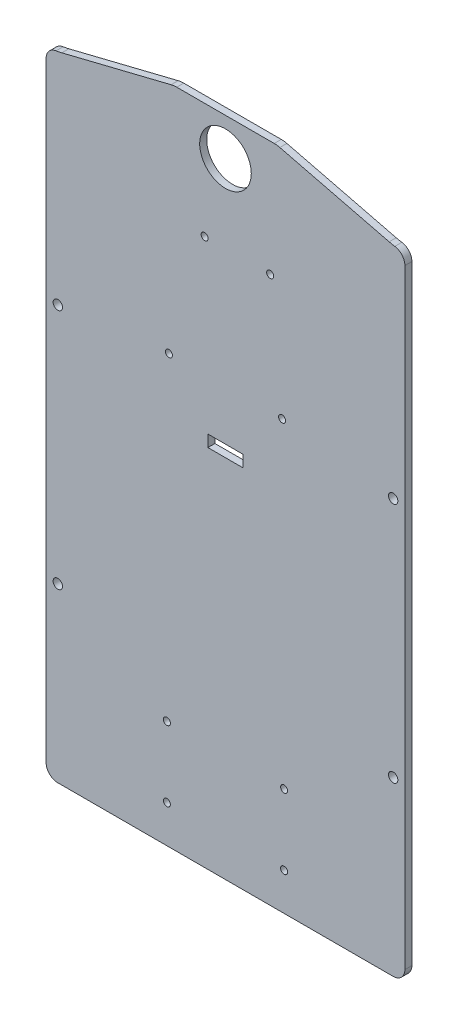
SolidWorks part; units mm, degrees
ref_plane "Alzado" through (0, 0, 0) normal (0, 0, 1) x (1, 0, 0)
ref_plane "Planta" through (0, 0, 0) normal (0, 1, 0) x (1, 0, 0)
ref_plane "Vista lateral" through (0, 0, 0) normal (1, 0, 0) x (0, 0, -1)
sketch "Croquis1" plane through (0, 0, 0) normal (0, 0, 1) x (1, 0, 0)
  line L1 (-76.5, 135) -> (76.5, 135)
  line L2 (-76.5, 135) -> (-76.5, -135)
  line L3 (-76.5, -135) -> (76.5, -135)
  line L4 (76.5, 135) -> (76.5, -135)
  line L5 (-76.5, 135) -> (76.5, -135) construction
  line L6 (-76.5, -135) -> (76.5, 135) construction
  point P0 (0, 0)
  dimension "D1" = 270
  dimension "D2" = 153
extrude "Saliente-Extruir1" add sketch "Croquis1" along normal blind 3
sketch "Croquis2" plane through (0, 0, 3) normal (0, 0, 1) x (1, 0, 0)
  line L0 (0, 135) -> (0, -135) construction
  line L1 (76.5, 135) -> (-76.5, 135) construction
  line L2 (-76.5, -135) -> (76.5, -135) construction
  line L3 (-76.5, 0) -> (-76.5, -10) construction
  line L4 (-76.5, 135) -> (-76.5, -135) construction
  line L5 (-76.5, 110) -> (0, 110) construction
  line L6 (-76.5, 0) -> (-76.5, 41.5) construction
  line L7 (-76.5, 41.5) -> (-71.5, 41.5) construction
  line L8 (76.5, -135) -> (76.5, 135) construction
  line L10 (0, -10) -> (76.5, -10) construction
  circle A8 centre (-71.5, 41.5) radius 2
  circle A9 centre (-71.5, -61.5) radius 2
  circle A10 centre (71.5, -61.5) radius 2
  circle A11 centre (71.5, 41.5) radius 2
  dimension "D2" = 4
  dimension "D6" = 51.5
  dimension "D1" = 125
  dimension "D3" = 5
  dimension "D4" = 5
  dimension "D5" = 5
extrude "Cortar-Extruir1" cut sketch "Croquis2" against normal through all
fillet "Redondeo1" radius 5 4 edges at (-76.5, -135, 1.5) (76.5, -135, 1.5) (76.5, 135, 1.5) (-76.5, 135, 1.5)
sketch "Croquis4" plane through (0, 0, 3) normal (0, 0, 1) x (1, 0, 0)
  line L0 (0, 0) -> (76.5, 0) construction
  line L1 (76.5, -130) -> (76.5, 130) construction
  line L2 (0, 0) -> (0, 135) construction
  line L3 (71.5, 135) -> (-71.5, 135) construction
  line L4 (-60, 113.7625) -> (-60, 106.2375) construction
  line L5 (-60, 110) -> (0, 110) construction
  line L6 (-76.5, 130) -> (-76.5, -130) construction
  line L7 (-76.5, 114.7625) -> (76.5, 114.7625) construction
  line L8 (-76.5, 114.7625) -> (-76.5, 105.2375) construction
  line L9 (-76.5, 105.2375) -> (76.5, 105.2375) construction
  line L10 (76.5, 114.7625) -> (76.5, 105.2375) construction
  line L11 (-76.5, 114.7625) -> (76.5, 105.2375) construction
  line L12 (-76.5, 105.2375) -> (76.5, 114.7625) construction
  line L13 (0, 135) -> (0, 147.2375) construction
  line L14 (22, 147.2375) -> (-22, 147.2375)
  line L15 (-22, 147.2375) -> (-71.5, 135)
  line L16 (22, 147.2375) -> (71.5, 135)
  line L17 (-71.5, 135) -> (71.5, 135)
  circle A0 centre (0, 129.7625) radius 11 construction
  dimension "D2" = 22
  dimension "D1" = 9.525
  dimension "D3" = 42
  dimension "D4" = 15
  dimension "D5" = 22
extrude "Saliente-Extruir2" add sketch "Croquis4" against normal up to surface (3 mm away) up to face at (69.5, 41.5, 0)
fillet "Redondeo2" radius 25 2 edges at (71.5, 135, 1.5) (-71.5, 135, 1.5)
fillet "Redondeo3" radius 10 2 edges at (22, 147.2375, 1.5) (-22, 147.2375, 1.5)
sketch "Croquis5" plane through (0, 0, 3) normal (0, 0, 1) x (1, 0, 0)
  line L0 (0, 0) -> (0, 147.2375) construction
  line L1 (20.7822, 147.2375) -> (-20.7822, 147.2375) construction
  line L2 (-60, 113.7625) -> (-60, 106.2375) construction
  line L3 (-60, 110) -> (0, 110) construction
  line L4 (-76.5, 130) -> (-76.5, -130) construction
  line L5 (-76.5, 114.7625) -> (76.5, 114.7625) construction
  line L6 (-76.5, 114.7625) -> (-76.5, 105.2375) construction
  line L7 (-76.5, 105.2375) -> (76.5, 105.2375) construction
  line L8 (76.5, 114.7625) -> (76.5, 105.2375) construction
  line L9 (-76.5, 114.7625) -> (76.5, 105.2375) construction
  line L10 (-76.5, 105.2375) -> (76.5, 114.7625) construction
  line L12 (-20, 146.2375) -> (20, 146.2375) construction
  line L13 (-20, 146.2375) -> (-20, 116.2375) construction
  line L14 (-20, 116.2375) -> (20, 116.2375) construction
  line L15 (20, 146.2375) -> (20, 116.2375) construction
  line L16 (-20, 146.2375) -> (20, 116.2375) construction
  line L17 (-20, 116.2375) -> (20, 146.2375) construction
  circle A0 centre (0, 131.2375) radius 11
  dimension "D2" = 26
  dimension "D3" = 22
  dimension "D1" = 9.525
  dimension "D4" = 30
  dimension "D5" = 40
extrude "Cortar-Extruir3" cut sketch "Croquis5" against normal through all
sketch "Croquis6" plane through (0, 0, 3) normal (0, 0, 1) x (1, 0, 0)
  line L0 (24.13, 98.0201) -> (24.13, 47.2201) construction
  line L1 (0, 147.2375) -> (0, 0) construction
  line L2 (20.7822, 147.2375) -> (-20.7822, 147.2375) construction
  line L3 (-24.13, 47.2201) -> (24.13, 47.2201) construction
  line L5 (-7.5, 25.7977) -> (7.5, 25.7977)
  line L6 (-7.5, 25.7977) -> (-7.5, 20.7977)
  line L7 (-7.5, 20.7977) -> (7.5, 20.7977)
  line L8 (7.5, 25.7977) -> (7.5, 20.7977)
  circle A0 centre (-8.89, 98.0201) radius 1.5
  circle A1 centre (19.05, 98.0201) radius 1.5
  circle A2 centre (24.13, 47.2201) radius 1.5
  circle A3 centre (-24.13, 47.2201) radius 1.5
  point P13 (0, 47.2201)
  point P19 (0, 20.7977)
  dimension "D1" = 27.94
  dimension "D3" = 48.26
  dimension "D5" = 3
  dimension "D6" = 3
  dimension "D7" = 3
  dimension "D8" = 3
  dimension "D2" = 5.08
  dimension "D4" = 50.8
  dimension "D9" = 15
  dimension "D10" = 5
extrude "Cortar-Extruir4" cut sketch "Croquis6" against normal through all
sketch "Croquis7" plane through (0, 0, 3) normal (0, 0, 1) x (1, 0, 0)
  line L0 (0, 147.2375) -> (0, -135) construction
  line L1 (-25, -89.0384) -> (25, -89.0384) construction
  line L2 (-25, -89.0384) -> (-25, -119.0384) construction
  line L3 (-25, -119.0384) -> (25, -119.0384) construction
  line L4 (25, -89.0384) -> (25, -119.0384) construction
  line L5 (20.7822, 147.2375) -> (-20.7822, 147.2375) construction
  line L6 (-71.5, -135) -> (71.5, -135) construction
  circle A0 centre (-25, -89.0384) radius 1.5
  circle A1 centre (25, -89.0384) radius 1.5
  circle A2 centre (-25, -119.0384) radius 1.5
  circle A3 centre (25, -119.0384) radius 1.5
  point P10 (0, -89.0384)
  dimension "D1" = 50
  dimension "D2" = 30
extrude "Cortar-Extruir5" cut sketch "Croquis7" against normal blind 10
sketch "Croquis8" plane through (0, 0, 3) normal (0, 0, 1) x (1, 0, 0)
  line L0 (-76.5, 0) -> (0, 0) construction
  line L1 (-76.5, 130) -> (-76.5, -130) construction
  line L2 (0, 0) -> (0, 120.2375) construction
  line L4 (-82.5, 129.7743) -> (82.5, 129.7743) construction
  line L5 (-82.5, 129.7743) -> (-82.5, -129.7743) construction
  line L6 (-82.5, -129.7743) -> (82.5, -129.7743) construction
  line L7 (82.5, 129.7743) -> (82.5, -129.7743) construction
  line L8 (-82.5, 129.7743) -> (82.5, -129.7743) construction
  line L9 (-82.5, -129.7743) -> (82.5, 129.7743) construction
  line L10 (76.5, -130) -> (76.5, 130) construction
  circle A0 centre (0, 131.2375) radius 11 construction
  circle A1 centre (71.5, 41.5) radius 2 construction
  point P18 (71.5, 41.5)
  dimension "D2" = 11
  dimension "D1" = 165
  dimension "D3" = 5
